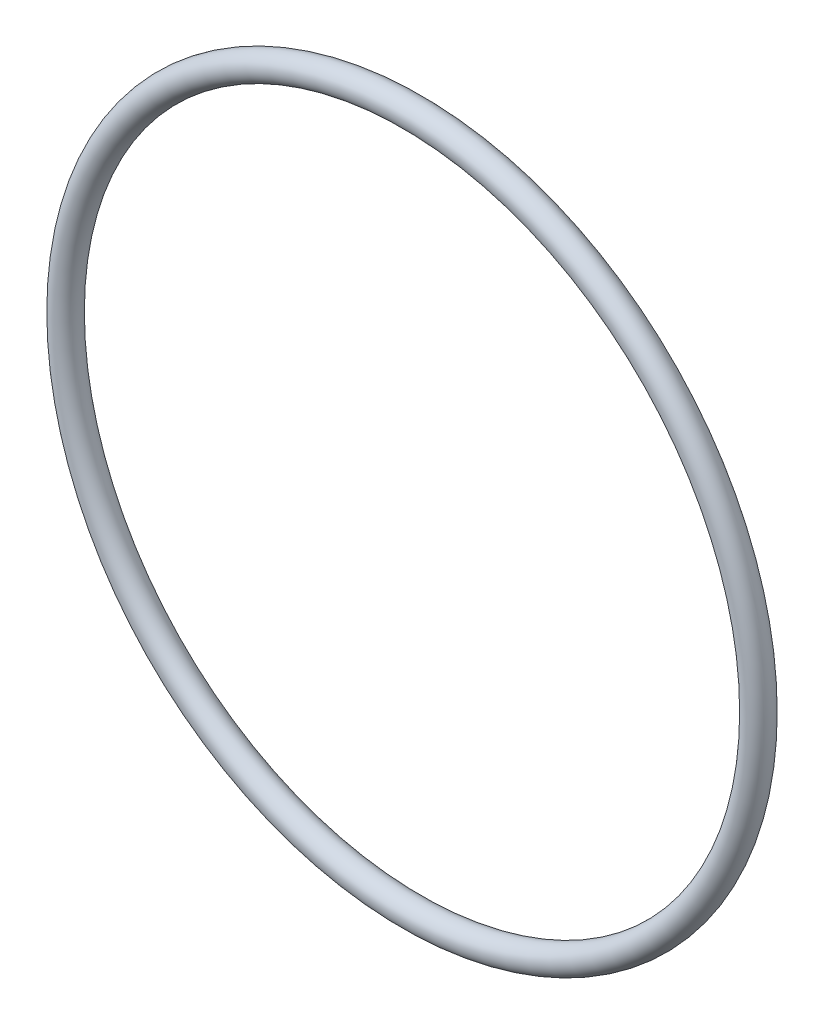
SolidWorks part; units mm, degrees
ref_plane "Front" through (0, 0, 0) normal (0, 0, 1) x (1, 0, 0)
ref_plane "Top" through (0, 0, 0) normal (0, 1, 0) x (1, 0, 0)
ref_plane "Right" through (0, 0, 0) normal (1, 0, 0) x (0, 0, -1)
sketch "Sketch1" plane through (0, 0, 0) normal (1, 0, 0) x (0, -1, 0)
  line L0 (0, -1.7653) -> (0, 1.7653) construction
  line L2 (-52.5551, 0) -> (52.5551, 0) construction
  line L3 (-44.2468, 0) -> (44.2468, 0) construction
  circle A0 centre (46.0121, 0) radius 1.7653
  point P9 (44.2468, 0)
  point P10 (47.7774, 0)
  point P13 (46.0121, 1.7653)
  point P14 (46.0121, -1.7653)
  dimension "Width" = 3.5306
  dimension "ID" = 88.4936
revolve "Revolve1" add sketch "Sketch1" angle 360 about L0
